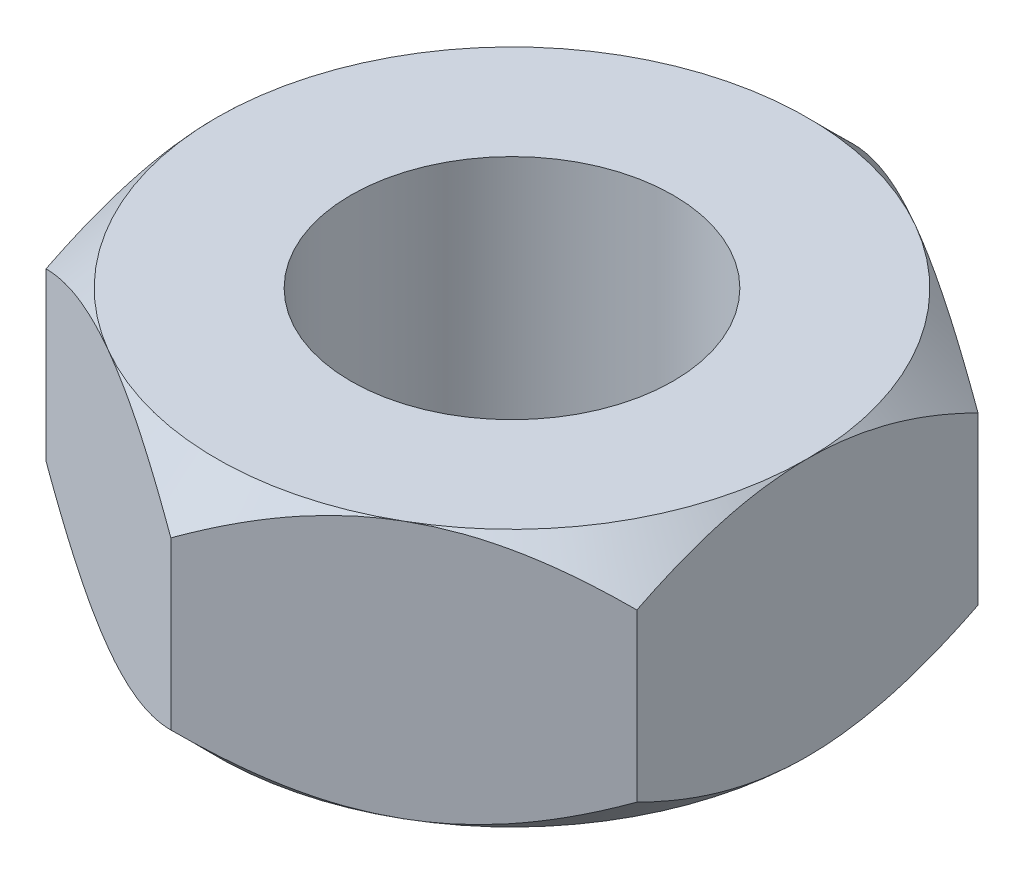
SolidWorks part; units mm, degrees
material "1023 Carbon Steel Sheet (SS)"
ref_plane "Front Plane" through (0, 0, 0) normal (0, 0, 1) x (1, 0, 0)
ref_plane "Top Plane" through (0, 0, 0) normal (0, 1, 0) x (1, 0, 0)
ref_plane "Right Plane" through (0, 0, 0) normal (1, 0, 0) x (0, 0, -1)
sketch "Sketch1" plane through (0, 0, 0) normal (0, 1, 0) x (1, 0, 0)
  line L1 (0, 3.1754) -> (-2.75, 1.5877)
  line L2 (-2.75, 1.5877) -> (-2.75, -1.5877)
  line L3 (-2.75, -1.5877) -> (0, -3.1754)
  line L4 (0, -3.1754) -> (2.75, -1.5877)
  line L5 (2.75, -1.5877) -> (2.75, 1.5877)
  line L6 (2.75, 1.5877) -> (0, 3.1754)
  circle A0 centre (0, 0) radius 2.75 construction
  circle A1 centre (0, 0) radius 1.5
  dimension "D2" = 3
  dimension "D1" = 5.5
extrude "Boss-Extrude1" add sketch "Sketch1" along normal blind 2.4
sketch "Sketch2" plane through (0, 2.4, 0) normal (0, 1, 0) x (1, 0, 0)
  circle A0 centre (0, 0) radius 2.75
  dimension "D1" = 5.5
extrude "Cut-Extrude1" cut sketch "Sketch2" against normal through all draft 45 flip side to cut
sketch "Sketch3" plane through (0, 0, 0) normal (0, -1, 0) x (1, 0, 0)
  circle A0 centre (0, 0) radius 2.75
  dimension "D1" = 5.5
extrude "Cut-Extrude2" cut sketch "Sketch3" against normal through all draft 45 flip side to cut
